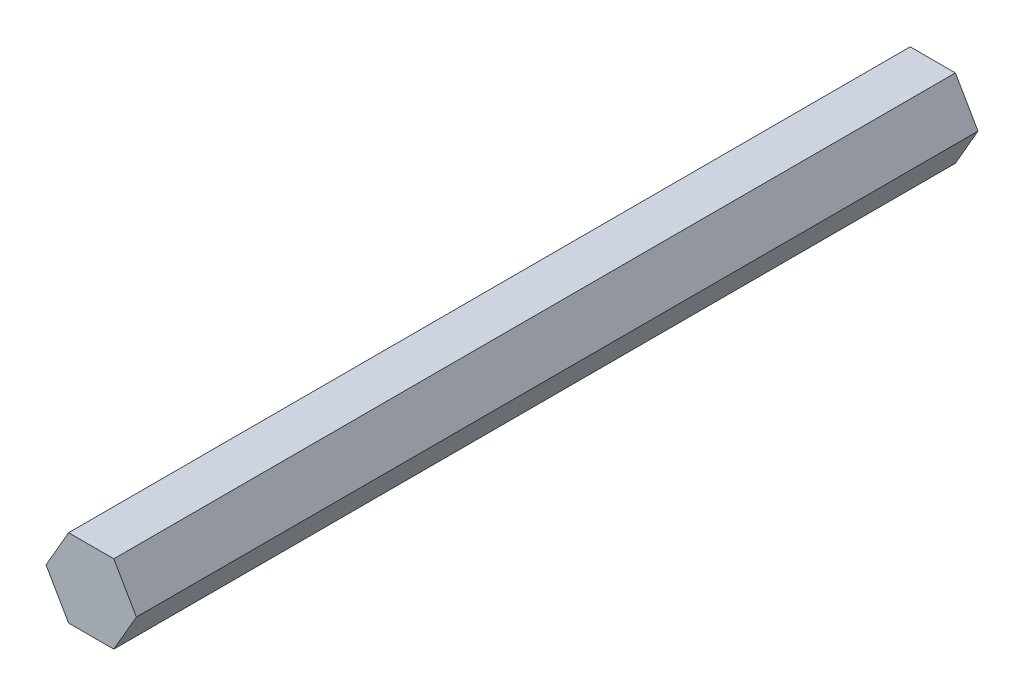
SolidWorks part; units mm, degrees
material "6061-T6 (SS)"
ref_plane "Front" through (0, 0, 0) normal (0, 0, 1) x (1, 0, 0)
ref_plane "Top" through (0, 0, 0) normal (0, 1, 0) x (1, 0, 0)
ref_plane "Right" through (0, 0, 0) normal (1, 0, 0) x (0, 0, -1)
sketch "Sketch1" plane through (0, 0, 0) normal (0, 0, 1) x (1, 0, 0)
  line L1 (3.6662, 6.35) -> (-3.6662, 6.35)
  line L2 (-3.6662, 6.35) -> (-7.3323, 0)
  line L3 (-7.3323, 0) -> (-3.6662, -6.35)
  line L4 (-3.6662, -6.35) -> (3.6662, -6.35)
  line L5 (3.6662, -6.35) -> (7.3323, 0)
  line L6 (7.3323, 0) -> (3.6662, 6.35)
  circle A0 centre (0, 0) radius 6.35 construction
  dimension "D1" = 12.7
extrude "Boss-Extrude1" add sketch "Sketch1" along normal blind 136.525
sketch "Sketch4" plane through (0, 0, 0) normal (0, 0, -1) x (-1, 0, 0)
  point P0 (0, 0)
hole_wizard "#10-32 Tapped Hole1" positions "Sketch4" profile "Sketch3" tap size "#10-32" standard "ANSI Inch"
cosmetic thread "Hole Thread1" parameters "D1"=127, "D2"=4.826
sketch "Sketch3" plane through (0, 0, 0) normal (1, 0, 0) x (0, 1, 0)
  line L0 (0, 0) -> (0, 13.9133)
  line L1 (0, 13.9133) -> (2.0193, 12.7)
  line L2 (2.0193, 12.7) -> (2.0193, 0)
  line L5 (2.0193, 0) -> (0, 0)
  line L10 (0, 13.9133) -> (-2.0193, 12.7) construction
  line L11 (0, -6.35) -> (0, 107.95) construction
  dimension "Tap Drill Dia." = 4.0386
  dimension "Tap Drill Depth" = 12.7
  dimension "Drill Angle" = 118
